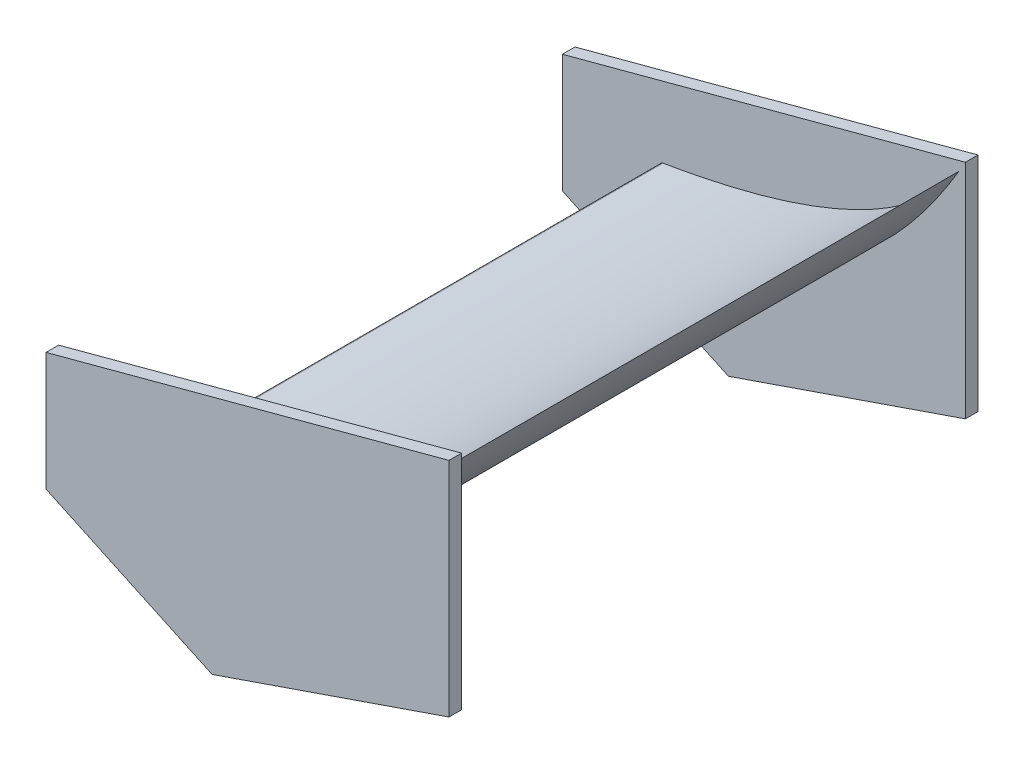
SolidWorks part; units mm, degrees
ref_plane "Front Plane" through (0, 0, 0) normal (0, 0, 1) x (1, 0, 0)
ref_plane "Top Plane" through (0, 0, 0) normal (0, 1, 0) x (1, 0, 0)
ref_plane "Right Plane" through (0, 0, 0) normal (1, 0, 0) x (0, 0, -1)
sketch "Sketch2" plane through (0, 0, 0) normal (0, 0, 1) x (1, 0, 0)
  line L0 (0, 0) -> (0, 903)
  line L3 (0, 903) -> (800, 240)
  line L4 (800, 240) -> (0, 240)
  circle A0 centre (510, 166.5) radius 256.5
  dimension "D6" = 513
  dimension "D1" = 903
  dimension "D2" = 800
  dimension "D3" = 240
  dimension "D4" = 73.5
  dimension "D5" = 290
sketch "Sketch3" plane through (0, 0, 0) normal (0, 0, 1) x (1, 0, 0)
  line L1 (0, 0) -> (980.2772, 0) construction
  line L2 (980.2772, 0) -> (980.2772, 500) construction
  line L3 (980.2772, 500) -> (0, 500) construction
  line L4 (0, 500) -> (0, 0) construction
  line L5 (980.2772, -96.8884) -> (980.2772, 1103.1116) construction
  line L6 (980.2772, 1103.1116) -> (60.2772, 1103.1116) construction
  line L14 (980.2772, 500) -> (183.7404, 500)
  line L16 (510, 500) -> (980.2772, 661.9294)
  line L18 (180.2772, 653.7523) -> (510, 500)
  line L19 (180.2772, 888.7523) -> (180.2772, 653.7523)
  line L20 (980.2772, 1103.1116) -> (180.2772, 888.7523)
  line L21 (980.2772, 1103.1116) -> (980.2772, 661.9294)
  circle A1 centre (510, 166.5) radius 256.5 construction
  point P0 (510, -90)
  dimension "D10" = 513
  dimension "D1" = 500
  dimension "D2" = 470.2772
  dimension "D3" = 1200
  dimension "D4" = 920
  dimension "D5" = 800
  dimension "D6" = 235
  dimension "D7" = 75
  dimension "D8" = 19
  dimension "D9" = 25
  dimension "D11" = 510
extrude "Boss-Extrude4" add sketch "Sketch3" along normal blind 25 from offset 500 contours L21 L20 L19 L18 L16
mirror "Mirror6" about plane through (0, 0, 0) normal (0, 0, 1) of bodies 104
sketch "Sketch4" plane through (0, 0, 0) normal (0, 0, 1) x (1, 0, 0)
  line L0 (980.2772, 1103.1116) -> (980.2772, 500) construction
  line L3 (980.2772, 500) -> (980.2772, 801.5558) construction
  line L4 (980.2772, 801.5558) -> (526.0353, 801.5558) construction
  line L5 (980.2772, 661.9294) -> (980.2772, 1103.1116)
  line L6 (510, 500) -> (980.2772, 661.9294)
  line L7 (180.2772, 653.7523) -> (510, 500)
  line L8 (180.2772, 888.7523) -> (180.2772, 653.7523)
  line L9 (980.2772, 1103.1116) -> (180.2772, 888.7523)
  line L10 (980.2772, 661.9294) -> (980.2772, 1103.1116)
  line L11 (510, 500) -> (980.2772, 661.9294)
  line L12 (180.2772, 653.7523) -> (510, 500)
  line L13 (180.2772, 888.7523) -> (180.2772, 653.7523)
  line L14 (980.2772, 1103.1116) -> (180.2772, 888.7523)
  line L17 (980.2772, 1103.1116) -> (861.8747, 881.5558) construction
  line L18 (861.8747, 881.5558) -> (380.2772, 801.5558) construction
  arc A0 (380.2772, 801.5558) -> (375.3372, 791.1939) centre (381.4243, 794.6504) ccw
  spline S0 degree 2 poles (980.2772, 1103.1116) (861.8747, 881.5558) (380.2772, 801.5558) knots 0 0 0 1 1 1
  spline S1 degree 2 poles (375.3372, 791.1939) (722.6295, 653.6363) (980.2772, 1103.1116) knots 0 0 0 1 1 1
  dimension "D2" = 753.7784
  dimension "D5" = 9.432
  dimension "D6" = 600
  dimension "D3" = 7
  dimension "D7" = 58.87
  dimension "D4" = 80
  dimension "D8" = 36.7503
  dimension "D9" = 6.0871
  dimension "D1" = 0
extrude "Boss-Extrude5" add sketch "Sketch4" along normal mid plane 1000 separate body contours A0 S1 S0
